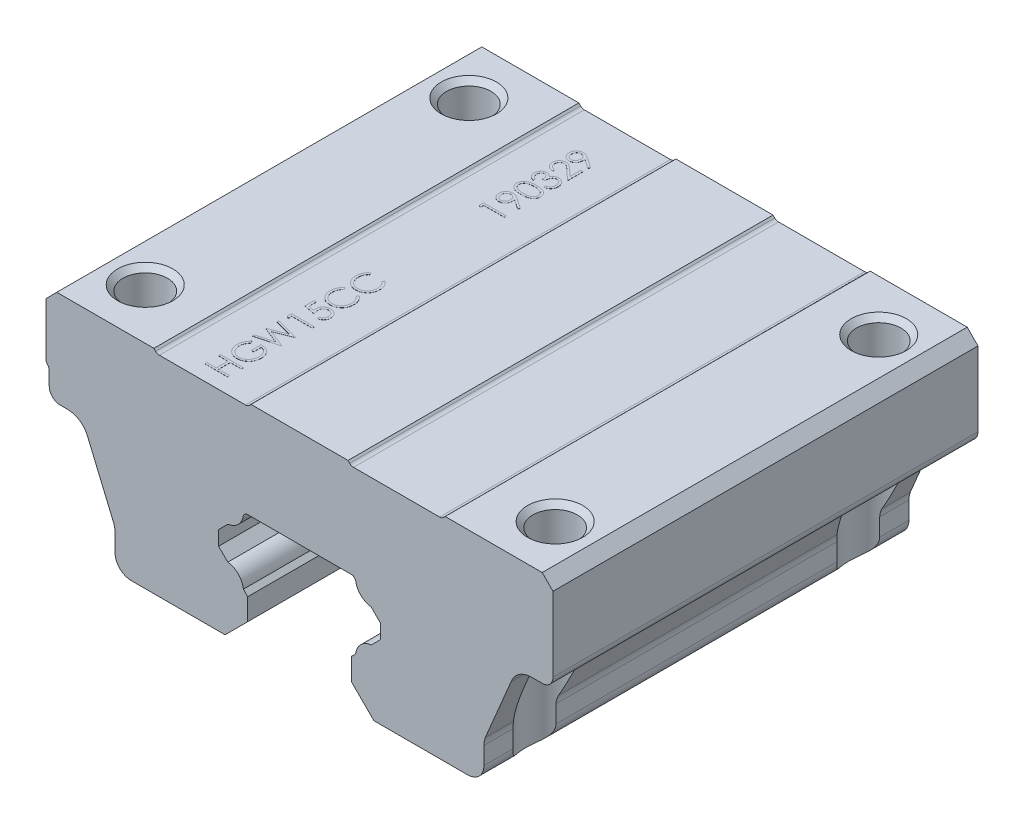
SolidWorks part; units mm, degrees
material "AISI Тип A2 Инструментальная сталь"
ref_plane "Спереди" through (0, 0, 0) normal (0, 0, 1) x (1, 0, 0)
ref_plane "Сверху" through (0, 0, 0) normal (0, 1, 0) x (1, 0, 0)
ref_plane "Справа" through (0, 0, 0) normal (1, 0, 0) x (0, 0, -1)
sketch "Model" plane through (0, 0, 0) normal (0, 0, 1) x (1, 0, 0)
  line L18 (15.2, 0) -> (15.5982, 0)
  line L19 (17.0982, 1.4984) -> (17.1, 3.1221)
  line L20 (17.2206, 3.8061) -> (19.6147, 9.484)
  line L21 (21.4941, 10.8) -> (22.5, 10.8)
  line L22 (23.5, 11.8) -> (23.5, 18.6929)
  line L23 (23.5, 18.6929) -> (22.5, 19.7)
  line L24 (22.5, 19.7) -> (13.5, 19.7)
  line L25 (13.5, 19.7) -> (13.3465, 19.5464)
  line L26 (12.9929, 19.4) -> (5.0071, 19.4)
  line L27 (4.6536, 19.5464) -> (4.5, 19.7)
  line L28 (4.5, 19.7) -> (-4.5, 19.7)
  line L29 (-4.5, 19.7) -> (-4.6536, 19.5464)
  line L30 (-5.0071, 19.4) -> (-12.9929, 19.4)
  line L31 (-13.3444, 19.5444) -> (-13.5, 19.7)
  line L32 (-13.5, 19.7) -> (-22.5, 19.7)
  line L33 (-22.5, 19.7) -> (-23.5, 18.6929)
  line L34 (-23.5, 18.6929) -> (-23.5, 13.7)
  line L35 (-23.5, 13.7) -> (-23.3464, 13.4465)
  line L36 (-23.2, 13.0929) -> (-23.2, 11.8)
  line L37 (-22.2, 10.8) -> (-21.4941, 10.8)
  line L38 (-19.6147, 9.484) -> (-17.2206, 3.8062)
  line L39 (-17.1, 3.1222) -> (-17.0982, 1.4983)
  line L146 (4.7998, 2.0996) -> (6.8994, 0)
  line L147 (15.2, 0) -> (6.8994, 0)
  line L155 (-6.8994, 0) -> (-15.5982, 0)
  line L156 (-6.8994, 0) -> (-4.7998, 2.0996)
  line L157 (-4.7998, 2.0996) -> (-4.7998, 4.1091)
  line L158 (-4.7998, 4.1091) -> (-5.2008, 4.5101)
  line L159 (-6.6481, 5.9574) -> (-7.5, 6.8093)
  line L160 (-7.5, 6.8093) -> (-7.5, 8.1495)
  line L161 (-7.5, 8.1495) -> (-6.6345, 9.015)
  line L162 (-5.2023, 10.4472) -> (-4.9495, 10.7)
  line L163 (-4.9495, 10.7) -> (4.9495, 10.7)
  line L164 (4.9495, 10.7) -> (5.2023, 10.4472)
  line L165 (6.6345, 9.015) -> (7.5, 8.1495)
  line L166 (7.5, 8.1495) -> (7.5, 6.8093)
  line L167 (7.5, 6.8093) -> (6.6481, 5.9574)
  line L168 (5.2008, 4.5101) -> (4.7998, 4.1091)
  line L169 (4.7998, 4.1091) -> (4.7998, 2.0996)
  arc A0 (15.5982, 0) -> (17.0982, 1.4984) centre (15.5982, 1.5) ccw
  arc A1 (17.2206, 3.8061) -> (17.1, 3.1221) centre (19.0999, 3.1221) ccw
  arc A2 (21.4941, 10.8) -> (19.6147, 9.484) centre (21.4941, 8.8) ccw
  arc A3 (22.5, 10.8) -> (23.5, 11.8) centre (22.5, 11.8) ccw
  arc A4 (12.9929, 19.4) -> (13.3465, 19.5464) centre (12.9929, 19.9) ccw
  arc A5 (4.6536, 19.5464) -> (5.0071, 19.4) centre (5.0071, 19.9) ccw
  arc A6 (-5.0071, 19.4) -> (-4.6536, 19.5464) centre (-5.0071, 19.9) ccw
  arc A7 (-13.3444, 19.5444) -> (-12.9929, 19.4) centre (-12.9957, 19.8931) ccw
  arc A8 (-23.2, 13.0929) -> (-23.3464, 13.4465) centre (-23.7, 13.0929) ccw
  arc A9 (-23.2, 11.8) -> (-22.2, 10.8) centre (-22.2, 11.8) ccw
  arc A10 (-19.6147, 9.484) -> (-21.4941, 10.8) centre (-21.4941, 8.8) ccw
  arc A11 (-17.1, 3.1222) -> (-17.2206, 3.8062) centre (-19.1, 3.1222) ccw
  arc A12 (-17.0982, 1.4983) -> (-15.5982, 0) centre (-15.5982, 1.5) ccw
  arc A13 (-5.2008, 4.5101) -> (-6.6481, 5.9574) centre (-6.8215, 4.3367) ccw
  arc A14 (-6.6345, 9.015) -> (-5.2023, 10.4472) centre (-6.8215, 10.6342) ccw
  arc A15 (5.2023, 10.4472) -> (6.6345, 9.015) centre (6.8215, 10.6342) ccw
  arc A16 (6.6481, 5.9574) -> (5.2008, 4.5101) centre (6.8215, 4.3367) ccw
extrude "Бобышка-Вытянуть1" add sketch "Model" along normal blind 39.4
sketch "Эскиз3" plane through (0, 10.8, 0) normal (0, -1, 0) x (1, 0, 0)
  line L0 (-23.5, 39.4) -> (-23.5, 0) construction
  line L4 (-22.2, 39.4) -> (-21.4941, 39.4) construction
  line L5 (-22.2, 0) -> (-21.4941, 0) construction
  line L6 (23.5, 39.4) -> (23.5, 0) construction
  circle A0 centre (-19, 34.7) radius 2.75
  circle A1 centre (-19, 4.7) radius 2.75
  circle A2 centre (19, 4.7) radius 2.75
  circle A3 centre (19, 34.7) radius 2.75
  dimension "D1" = 4.5
  dimension "D3" = 4.7
  dimension "D4" = 4.5
  dimension "D2" = 4.7
extrude "Вырез-Вытянуть1" cut sketch "Эскиз3" along normal through all
sketch "Эскиз4" plane through (0, 10.8, 0) normal (0, -1, 0) x (1, 0, 0)
  circle A0 centre (-19, 34.7) radius 2.06
  circle A1 centre (19, 34.7) radius 2.06
  circle A2 centre (-19, 4.7) radius 2.06
  circle A3 centre (19, 4.7) radius 2.06
extrude "Вырез-Вытянуть2" cut sketch "Эскиз4" against normal through all
sketch "Эскиз5" plane through (0, 19.4, 0) normal (0, 1, 0) x (1, 0, 0)
  line L0 (-8.0757, -38.2549) -> (-8.0757, -1.4664) construction
  text T0 "HGW15CC            190329" font "Century Gothic" height in points 8
extrude "Бобышка-Вытянуть2" add sketch "Эскиз5" along normal blind 0.01
chamfer "Фаска1" distance 0.5 angle 45 4 edges at (-19, 19.7, 32.64) (-19, 19.7, 2.64) (19, 19.7, 2.64) (19, 19.7, 32.64)
